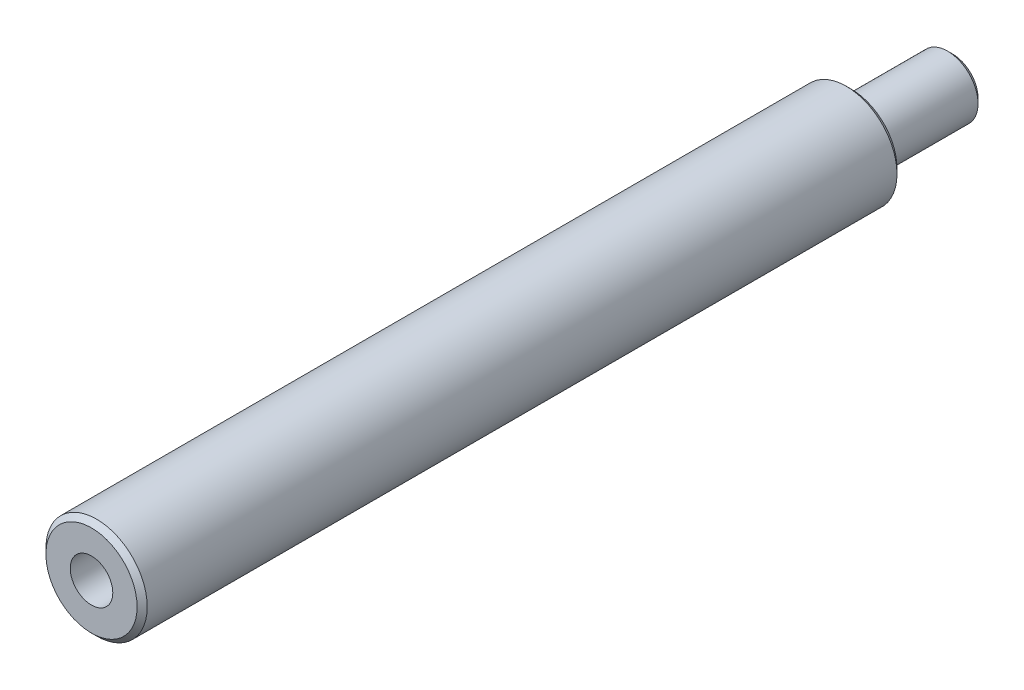
SolidWorks part; units mm, degrees
material "Alumine"
ref_plane "Plan de face" through (0, 0, 0) normal (0, 0, 1) x (1, 0, 0)
ref_plane "Plan de dessus" through (0, 0, 0) normal (0, 1, 0) x (1, 0, 0)
ref_plane "Plan de droite" through (0, 0, 0) normal (1, 0, 0) x (0, 0, -1)
sketch "Esquisse1" plane through (0, 0, 0) normal (0, 0, 1) x (1, 0, 0)
  circle A0 centre (0, 0) radius 5
  dimension "D1" = 10
extrude "Boss.-Extru.1" add sketch "Esquisse1" along normal blind 75
sketch "Esquisse2" plane through (0, 0, 0) normal (0, 0, -1) x (-1, 0, 0)
  circle A0 centre (0, 0) radius 3
  dimension "D1" = 6
extrude "Boss.-Extru.2" add sketch "Esquisse2" along normal blind 10
hole_wizard "Trou pour taraudage pour trou taraudé M51" positions "Esquisse3" profile "Esquisse4" hole size "M5" standard "ISO"
sketch "Esquisse3" plane through (0, 0, 75) normal (0, 0, 1) x (1, 0, 0)
  point P0 (0, 0)
sketch "Esquisse4" plane through (0, 0, 75) normal (1, 0, 0) x (0, -1, 0)
  line L0 (0, 0) -> (0, 11.2618)
  line L1 (0, 11.2618) -> (2.1, 10)
  line L2 (2.1, 10) -> (2.1, 0)
  line L5 (2.1, 0) -> (0, 0)
  line L10 (0, 11.2618) -> (-2.1, 10) construction
  line L11 (0, -6.35) -> (0, 107.95) construction
  dimension "Diamètre du perçage" = 4.2
  dimension "Profondeur du perçage" = 10
  dimension "Angle de pointe" = 118
chamfer "Chanfrein1" distance 0.5 angle 45 3 edges at (5, 0, 0) (5, 0, 75) (-3, 0, -10)
